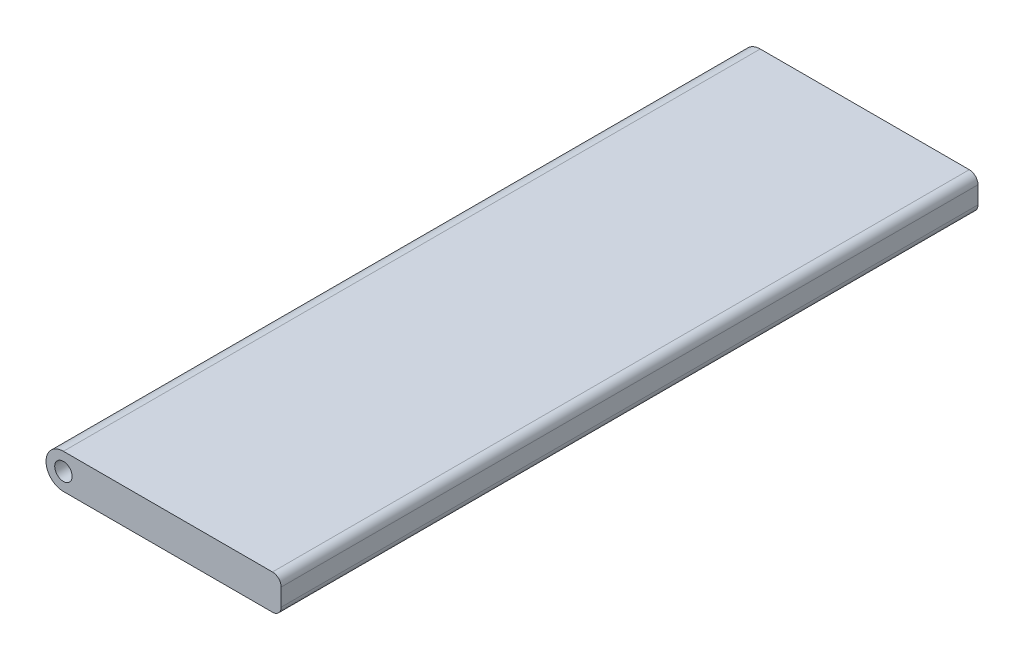
SolidWorks part; units mm, degrees
ref_plane "Front" through (0, 0, 0) normal (0, 0, 1) x (1, 0, 0)
ref_plane "Top" through (0, 0, 0) normal (0, 1, 0) x (1, 0, 0)
ref_plane "Right" through (0, 0, 0) normal (1, 0, 0) x (0, 0, -1)
sketch "草图1" plane through (0, 0, 0) normal (0, 0, 1) x (1, 0, 0)
  line L1 (0, -2) -> (24, -2)
  line L2 (0, -2) -> (0, 2)
  line L3 (0, 2) -> (24, 2)
  line L4 (25, -1) -> (25, 1)
  circle A0 centre (0, 0) radius 2
  arc A1 (24, 2) -> (25, 1) centre (24, 1) cw
  arc A2 (24, -2) -> (25, -1) centre (24, -1) ccw
  circle A3 centre (0, 0) radius 1
  point P11 (25, -2)
  dimension "D1" = 4
  dimension "D3" = 1
  dimension "D4" = 2
  dimension "D2" = 25
extrude "凸台-拉伸1" add sketch "草图1" along normal blind 80 contours A3 L2 A0 | A3 L2 A0 | L1 A2 L4 A1 L3 A0
